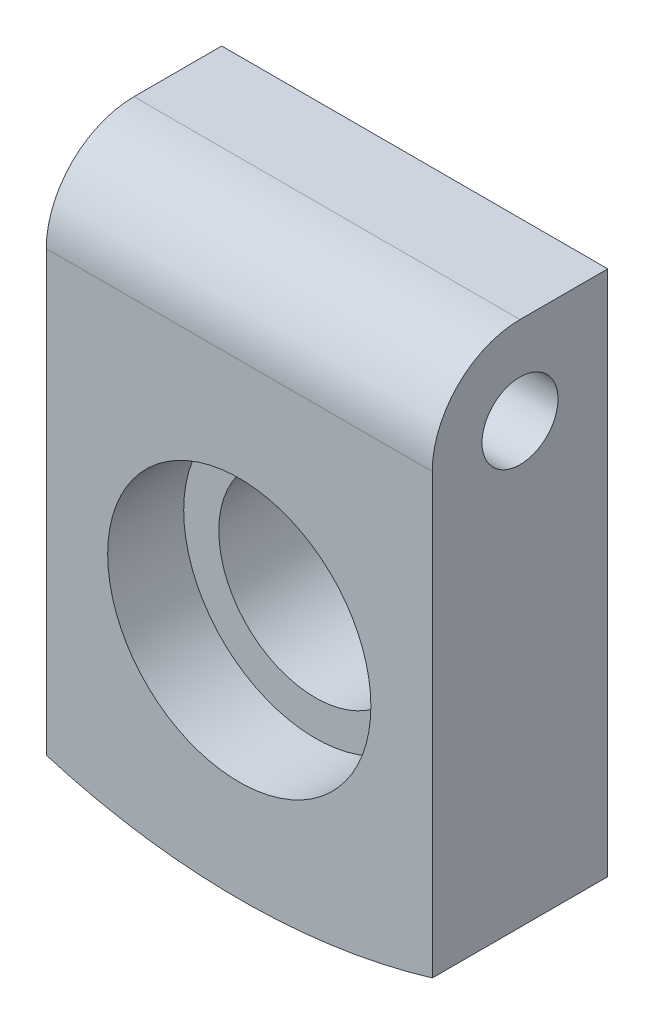
SolidWorks part; units mm, degrees
ref_plane "Front Plane" through (0, 0, 0) normal (0, 0, 1) x (1, 0, 0)
ref_plane "Top Plane" through (0, 0, 0) normal (0, 1, 0) x (1, 0, 0)
ref_plane "Right Plane" through (0, 0, 0) normal (1, 0, 0) x (0, 0, -1)
sketch "Sketch1" plane through (0, 0, 0) normal (0, 0, 1) x (1, 0, 0)
  line L0 (0, 0) -> (0, 90)
  line L5 (0, 90) -> (66, 90)
  line L6 (66, 90) -> (66, 0)
  arc A1 (0, 0) -> (66, 0) centre (33, 110.1635) ccw
  dimension "D3" = 90
  dimension "D1" = 115
  dimension "D2" = 66
extrude "Boss-Extrude1" add sketch "Sketch1" along normal blind 30
sketch "Sketch2" plane through (0, 0, 0) normal (0, 0, -1) x (-1, 0, 0)
  line L0 (-66, 90) -> (0, 90) construction
  circle A0 centre (-33, 35) radius 16.5
  arc A1 (-66, 0) -> (0, 0) centre (-33, 110.1635) ccw construction
  point P4 (0, 0)
  point P8 (-33, -4.8365)
  dimension "D1" = 33
  dimension "D2" = 55
extrude "Cut-Extrude1" cut sketch "Sketch2" against normal blind 17
sketch "Sketch3" plane through (0, 0, 17) normal (0, 0, -1) x (-1, 0, 0)
  circle A0 centre (-33, 35) radius 22.5
  dimension "D1" = 45
extrude "Cut-Extrude2" cut sketch "Sketch3" against normal up to next
fillet "Fillet2" radius 15 1 edges at (33, 90, 30)
sketch "Sketch4" plane through (0, 0, 0) normal (-1, 0, 0) x (0, 0, 1)
  circle A1 centre (15, 75) radius 6.5
  dimension "D1" = 13
extrude "Cut-Extrude3" cut sketch "Sketch4" against normal up to next
